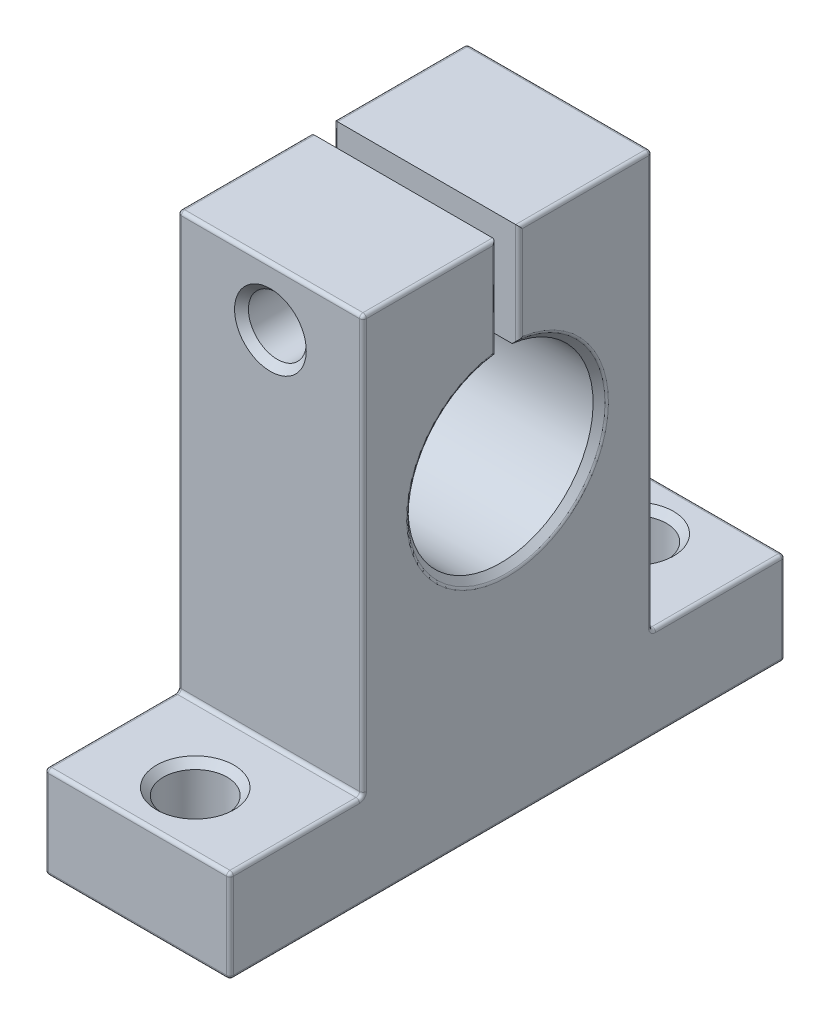
SolidWorks part; units mm, degrees
material "АМг 2 ГОСТ 4784-97"
ref_plane "Front Plane" through (0, 0, 0) normal (0, 0, 1) x (1, 0, 0)
ref_plane "Top Plane" through (0, 0, 0) normal (0, 1, 0) x (1, 0, 0)
ref_plane "Right Plane" through (0, 0, 0) normal (1, 0, 0) x (0, 0, -1)
sketch "Sketch1" plane through (0, 0, 0) normal (1, 0, 0) x (0, 0, -1)
  line L0 (-24, 0) -> (24, 0)
  line L1 (24, 0) -> (24, 8)
  line L2 (24, 8) -> (12.5, 8)
  line L3 (12.5, 8) -> (12.5, 44)
  line L4 (12.5, 44) -> (1, 44)
  line L5 (-12.5, 44) -> (-12.5, 8)
  line L6 (-12.5, 8) -> (-24, 8)
  line L7 (-24, 8) -> (-24, 0)
  line L8 (-1, 44) -> (-12.5, 44)
  line L9 (1, 34.9373) -> (1, 44)
  line L10 (-1, 34.9373) -> (-1, 44)
  line L11 (0, 0) -> (0, 50.015) construction
  arc A0 (-1, 34.9373) -> (1, 34.9373) centre (0, 27) ccw
  point P12 (1, 39.4686)
  dimension "D8" = 16
  dimension "D1" = 48
  dimension "D2" = 24
  dimension "D3" = 25
  dimension "D4" = 2
  dimension "D5" = 8
  dimension "D6" = 8
  dimension "D7" = 44
  dimension "D9" = 27
extrude "Boss-Extrude1" add sketch "Sketch1" along normal mid plane 16
sketch "Sketch2" plane through (0, 8, 0) normal (0, 1, 0) x (1, 0, 0)
  line L0 (13.7654, 0) -> (-15.2887, 0) construction
  line L1 (8, -12.5) -> (8, -24) construction
  circle A0 centre (0, -19) radius 2.75
  circle A1 centre (0, 19) radius 2.75
  dimension "D3" = 8
  dimension "D1" = 38
  dimension "D2" = 5.5
extrude "Cut-Extrude1" cut sketch "Sketch2" against normal through all
sketch "Sketch3" plane through (0, 0, -12.5) normal (0, 0, -1) x (-1, 0, 0)
  line L0 (-8, 44) -> (8, 44) construction
  circle A0 centre (0, 39) radius 2.5
  dimension "D2" = 5
  dimension "D1" = 5
extrude "Cut-Extrude2" cut sketch "Sketch3" against normal through all
sketch "Sketch4" plane through (0, 0, -12.5) normal (0, 0, -1) x (-1, 0, 0)
  circle A0 centre (0, 39) radius 4
  dimension "D1" = 8
extrude "Cut-Extrude3" cut sketch "Sketch4" against normal blind 5
chamfer "Фаска1" distance 0.6 angle 45 7 edges at (0, 0, -16.25) (0, 0, 21.75) (-4, 39, -12.5) (0, 8, -16.25) (0, 8, 21.75) (0, 41.5, 12.5) (8, 19, 0)
fillet "Скругление1" radius 0.3 32 edges at (-8, 0, 0) (-8, 4, -24) (-8, 8, -18.25) (-8, 26, -12.5) (-8, 44, -6.75) (-8, 39.4686, -1) (-8, 19, 0) (-8, 39.4686, 1) (-8, 44, 6.75) (-8, 26, 12.5) (-8, 8, 18.25) (-8, 4, 24) (8, 44, -6.75) (8, 26, -12.5) (8, 8, -18.25) (8, 4, -24) (8, 0, 0) (8, 4, 24) (8, 8, 18.25) (8, 26, 12.5) (8, 44, 6.75) (8, 39.7708, 1) (8, 18.4, 0) (8, 39.7708, -1) (0, 0, -24) (0, 8, -24) (0, 8, -12.5) (0, 44, -12.5) (0, 0, 24) (0, 44, 12.5) (0, 8, 12.5) (0, 8, 24)
